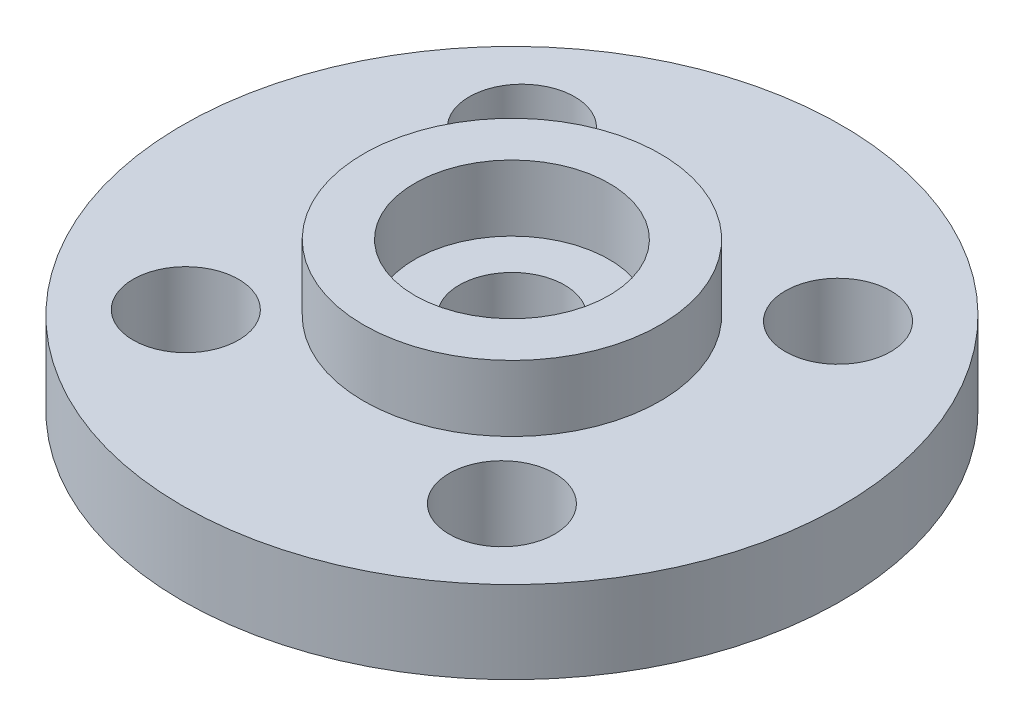
SolidWorks part; units mm, degrees
ref_plane "前视基准面" through (0, 0, 0) normal (0, 0, 1) x (1, 0, 0)
ref_plane "上视基准面" through (0, 0, 0) normal (0, 1, 0) x (1, 0, 0)
ref_plane "右视基准面" through (0, 0, 0) normal (1, 0, 0) x (0, 0, -1)
sketch "草图1" plane through (0, 0, 0) normal (0, 1, 0) x (1, 0, 0)
  circle A0 centre (0, 0) radius 10
  dimension "D1" = 20
extrude "凸台-拉伸1" add sketch "草图1" along normal blind 2.5
sketch "草图3" plane through (0, 2.5, 0) normal (0, 1, 0) x (1, 0, 0)
  circle A0 centre (-4.7952, 5.0996) radius 1.6
  circle A1 centre (-5.0996, -4.7952) radius 1.6
  circle A2 centre (4.7952, -5.0996) radius 1.6
  circle A3 centre (5.0996, 4.7952) radius 1.6
  circle A4 centre (0, 0) radius 1.6
  point P11 (0, 0)
  dimension "D3" = 3.2
  dimension "D4" = 3.2
  dimension "D2" = 14
  dimension "D1" = 4
extrude "切除-拉伸1" cut sketch "草图3" against normal through all
sketch "草图4" plane through (0, 2.5, 0) normal (0, 1, 0) x (1, 0, 0)
  circle A0 centre (0, 0) radius 4.5
  dimension "D1" = 9
extrude "凸台-拉伸2" add sketch "草图4" along normal blind 2
sketch "草图5" plane through (0, 4.5, 0) normal (0, 1, 0) x (1, 0, 0)
  circle A0 centre (0, 0) radius 2.95
  dimension "D1" = 5.9
extrude "切除-拉伸2" cut sketch "草图5" against normal blind 2
